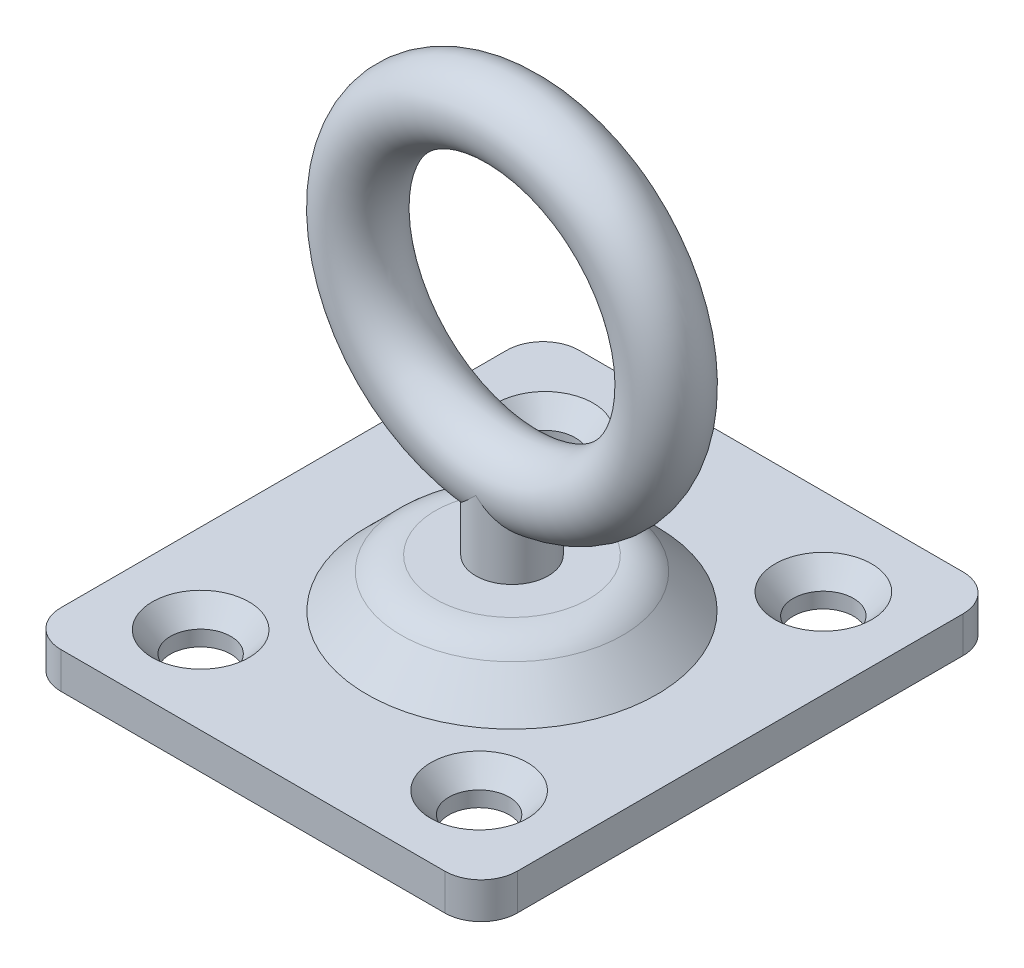
SolidWorks part; units mm, degrees
ref_plane "Front Plane" through (0, 0, 0) normal (0, 0, 1) x (1, 0, 0)
ref_plane "Top Plane" through (0, 0, 0) normal (0, 1, 0) x (1, 0, 0)
ref_plane "Right Plane" through (0, 0, 0) normal (1, 0, 0) x (0, 0, -1)
sketch "Sketch1" plane through (0, 0, 0) normal (0, 1, 0) x (1, 0, 0)
  line L0 (0, 17.018) -> (0, -17.018) construction
  line L1 (-12.6047, 17.018) -> (12.6047, 17.018)
  line L2 (-14.986, 14.6367) -> (-14.986, -14.6367)
  line L3 (-12.6047, -17.018) -> (12.6047, -17.018)
  line L4 (14.986, 14.6367) -> (14.986, -14.6367)
  line L5 (-14.986, 0) -> (14.986, 0) construction
  line L7 (-9.144, 11.303) -> (9.144, 11.303) construction
  line L8 (-9.144, 11.303) -> (-9.144, -11.303) construction
  line L9 (-9.144, -11.303) -> (9.144, -11.303) construction
  line L10 (9.144, 11.303) -> (9.144, -11.303) construction
  circle A0 centre (-9.144, 11.303) radius 1.9844 construction
  circle A1 centre (9.144, 11.303) radius 1.9844 construction
  circle A2 centre (9.144, -11.303) radius 1.9844 construction
  circle A3 centre (-9.144, -11.303) radius 1.9844 construction
  arc A4 (-12.6047, 17.018) -> (-14.986, 14.6367) centre (-12.6048, 14.6367) ccw
  arc A5 (12.6047, 17.018) -> (14.986, 14.6367) centre (12.6048, 14.6367) cw
  arc A6 (12.6047, -17.018) -> (14.986, -14.6367) centre (12.6048, -14.6367) ccw
  arc A7 (-14.986, -14.6367) -> (-12.6047, -17.018) centre (-12.6047, -14.6368) ccw
  point P12 (0, 11.303)
  point P13 (-9.144, 0)
  dimension "D5" = 3.9688
  dimension "D6" = 2.3813
  dimension "D1" = 34.036
  dimension "D2" = 29.972
  dimension "D3" = 22.606
  dimension "D4" = 18.288
extrude "Boss-Extrude1" add sketch "Sketch1" along normal blind 2.3813
sketch "Sketch2" plane through (0, 0, 0) normal (0, 1, 0) x (1, 0, 0)
  circle A0 centre (-9.144, 11.303) radius 1.9844 construction
  circle A1 centre (9.144, 11.303) radius 1.9844 construction
  circle A2 centre (9.144, -11.303) radius 1.9844 construction
  circle A3 centre (-9.144, -11.303) radius 1.9844 construction
  circle A4 centre (-9.144, 11.303) radius 1.9844
  circle A5 centre (9.144, 11.303) radius 1.9844
  circle A6 centre (9.144, -11.303) radius 1.9844
  circle A7 centre (-9.144, -11.303) radius 1.9844
extrude "Cut-Extrude1" cut sketch "Sketch2" along normal up to next
sketch "Sketch3" plane through (0, 2.3813, 0) normal (0, 1, 0) x (1, 0, 0)
  circle A0 centre (-9.144, 11.303) radius 3.175
  circle A1 centre (9.144, 11.303) radius 3.175
  circle A2 centre (9.144, -11.303) radius 3.175
  circle A3 centre (-9.144, -11.303) radius 3.175
  dimension "D1" = 6.35
extrude "Cut-Extrude2" cut sketch "Sketch3" against normal through all draft 41
sketch "Sketch4" plane through (0, 0, 0) normal (0, 0, 1) x (1, 0, 0)
  line L0 (0, 0) -> (0, 32.766) construction
  line L1 (0, 28.0035) -> (0, 32.766) construction
  line L2 (-9.525, 2.3812) -> (-7.2799, 4.6263)
  line L3 (-12.6047, 2.3813) -> (12.6047, 2.3813) construction
  line L4 (-5.0349, 5.5562) -> (0, 5.5562)
  line L5 (0, 5.5562) -> (0, 2.3813)
  line L6 (0, 2.3813) -> (-9.525, 2.3812)
  circle A0 centre (0, 20.2565) radius 12.5095 construction
  circle A1 centre (0, 20.2565) radius 7.747 construction
  circle A2 centre (0, 30.3847) radius 2.3813 construction
  arc A3 (-7.2799, 4.6263) -> (-5.0349, 5.5562) centre (-5.0349, 2.3812) cw
  point P17 (-6.35, 5.5562)
  dimension "D1" = 15.494
  dimension "D3" = 4.7625
  dimension "D7" = 3.175
  dimension "D2" = 32.766
  dimension "D4" = 19.05
  dimension "D5" = 12.7
  dimension "D6" = 3.175
revolve "Revolve1" add sketch "Sketch4" angle 360 mid plane about L0
sketch "Sketch5" plane through (0, 0, 0) normal (0, 0, 1) x (1, 0, 0)
  line L0 (0, 32.766) -> (0, 0) construction
  line L1 (0, 5.5562) -> (-2.3813, 5.5562)
  line L2 (-2.3813, 5.5562) -> (-2.3813, 3.175)
  line L3 (-2.3813, 5.5562) -> (-2.3813, 30.3847) construction
  line L4 (0, 30.3847) -> (-2.3813, 30.3847) construction
  line L5 (14.986, 2.3813) -> (14.986, 0) construction
  line L6 (-2.3813, 3.175) -> (-5.0349, 3.175)
  line L7 (-5.5961, 2.9425) -> (-7.8412, 0.6975)
  line L8 (-9.525, 2.3812) -> (-7.2799, 4.6263) construction
  line L10 (0, 0) -> (-9.525, 0)
  line L11 (0, 0) -> (0, 5.5562)
  circle A1 centre (0, 30.3847) radius 2.3813 construction
  arc A2 (-5.0349, 3.175) -> (-5.5961, 2.9425) centre (-5.0349, 2.3812) ccw
  arc A3 (-9.525, 0) -> (-7.8412, 0.6975) centre (-9.525, 2.3813) ccw
revolve "Cut-Revolve1" cut sketch "Sketch5" angle 360 mid plane about L0
sketch "Sketch6" plane through (0, 3.175, 0) normal (0, -1, 0) x (1, 0, 0)
  circle A0 centre (0, 0) radius 2.3813 construction
  circle A1 centre (0, 0) radius 2.3813
  circle A2 centre (0, 0) radius 4.7625
  dimension "D1" = 9.525
extrude "Boss-Extrude2" add sketch "Sketch6" along normal blind 1.1906 separate body
sketch "Sketch7" plane through (0, 0, 0) normal (0, 0, 1) x (1, 0, 0)
  line L0 (0, 32.766) -> (0, 0) construction
  line L1 (-2.3813, 10.1282) -> (-2.3813, 1.9844)
  line L2 (-2.3813, 5.5562) -> (-2.3813, 30.3847) construction
  line L3 (0, 12.5095) -> (0, 7.747) construction
  line L4 (-2.3813, 10.1282) -> (0, 10.1282)
  line L5 (-2.3813, 1.9844) -> (-3.175, 1.9844)
  line L6 (0, 10.1282) -> (0, 0.7937)
  circle A0 centre (0, 20.2565) radius 7.747 construction
  circle A1 centre (0, 20.2565) radius 12.5095 construction
  arc A2 (-3.175, 1.9844) -> (0, 0.7937) centre (0, 5.6224) ccw
  dimension "D1" = 1.1906
  dimension "D2" = 6.35
revolve "Revolve2" add sketch "Sketch7" angle 360 mid plane about L0
sketch "Sketch8" plane through (0, 0, 0) normal (0, 0, 1) x (1, 0, 0)
  line L0 (0, 20.2565) -> (0, 36.3675) construction
  circle A0 centre (0, 20.2565) radius 10.1283
sketch "Sketch9" plane through (0, 0, 0) normal (1, 0, 0) x (0, 0, -1)
  line L0 (0, 32.766) -> (0, 28.0035) construction
  circle A0 centre (0, 30.3847) radius 2.3813
sweep "Sweep1" add profiles "Sketch9" path "Sketch8"
